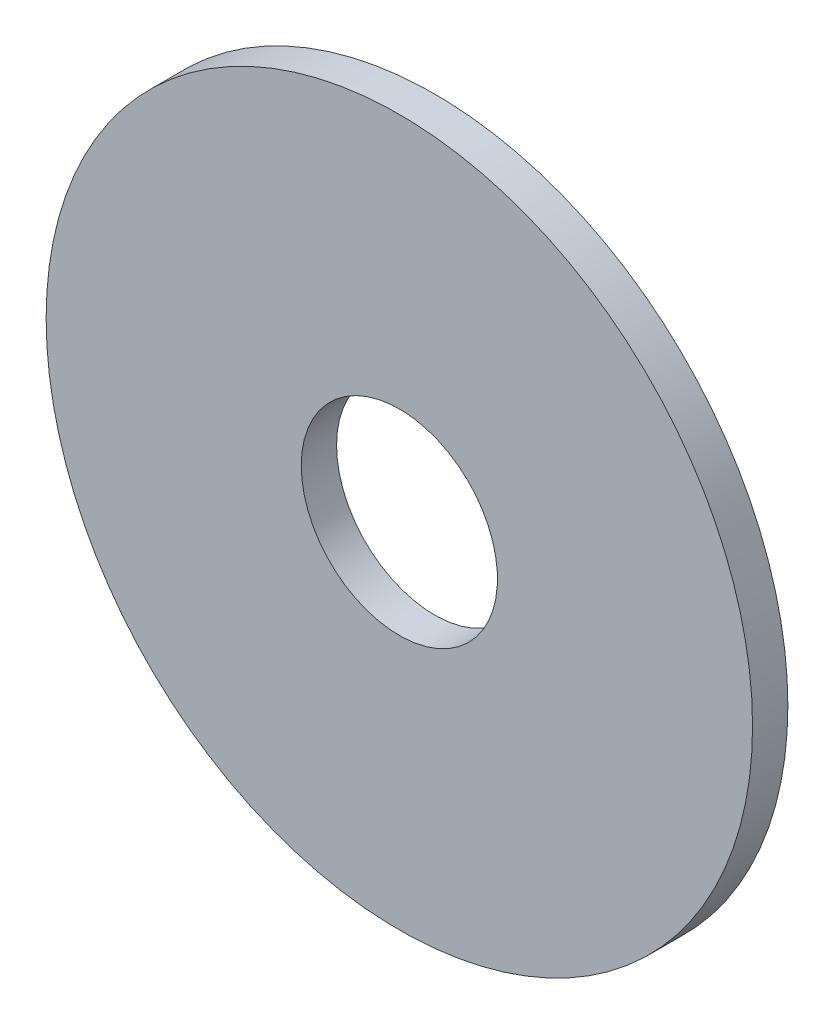
SolidWorks part; units mm, degrees
ref_plane "Front Plane" through (0, 0, 0) normal (0, 0, 1) x (1, 0, 0)
ref_plane "Top Plane" through (0, 0, 0) normal (0, 1, 0) x (1, 0, 0)
ref_plane "Right Plane" through (0, 0, 0) normal (1, 0, 0) x (0, 0, -1)
sketch "Sketch1" plane through (0, 0, 0) normal (0, 0, 1) x (1, 0, 0)
  circle A0 centre (0, 0) radius 60
  dimension "D1" = 120
extrude "Boss-Extrude1" add sketch "Sketch1" along normal blind 6
sketch "Sketch2" plane through (0, 0, 0) normal (0, 0, -1) x (-1, 0, 0)
  circle A0 centre (0, 0) radius 16.665
  dimension "D1" = 33.33
extrude "Cut-Extrude1" cut sketch "Sketch2" against normal through all
